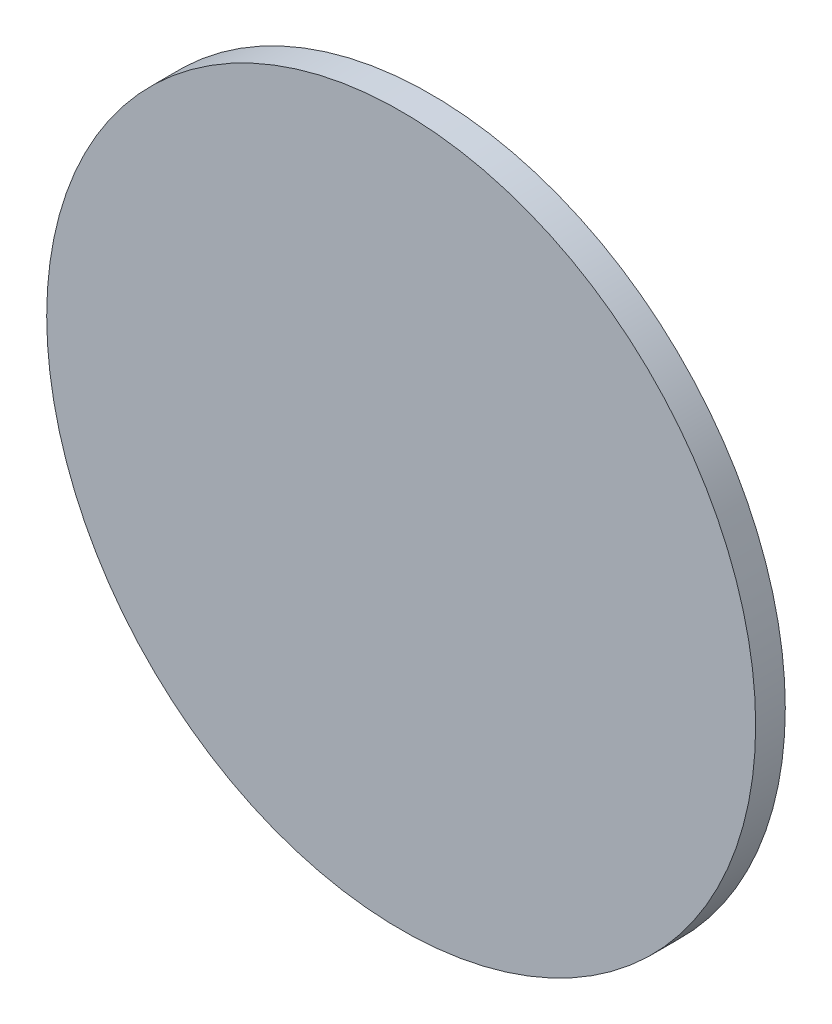
SolidWorks part; units mm, degrees
ref_plane "Front Plane" through (0, 0, 0) normal (0, 0, 1) x (1, 0, 0)
ref_plane "Top Plane" through (0, 0, 0) normal (0, 1, 0) x (1, 0, 0)
ref_plane "Right Plane" through (0, 0, 0) normal (1, 0, 0) x (0, 0, -1)
sketch "Sketch1" plane through (0, 0, 0) normal (0, 0, 1) x (1, 0, 0)
  circle A0 centre (0, 0) radius 75.946
extrude "Boss-Extrude1" add sketch "Sketch1" along normal blind 6.35
